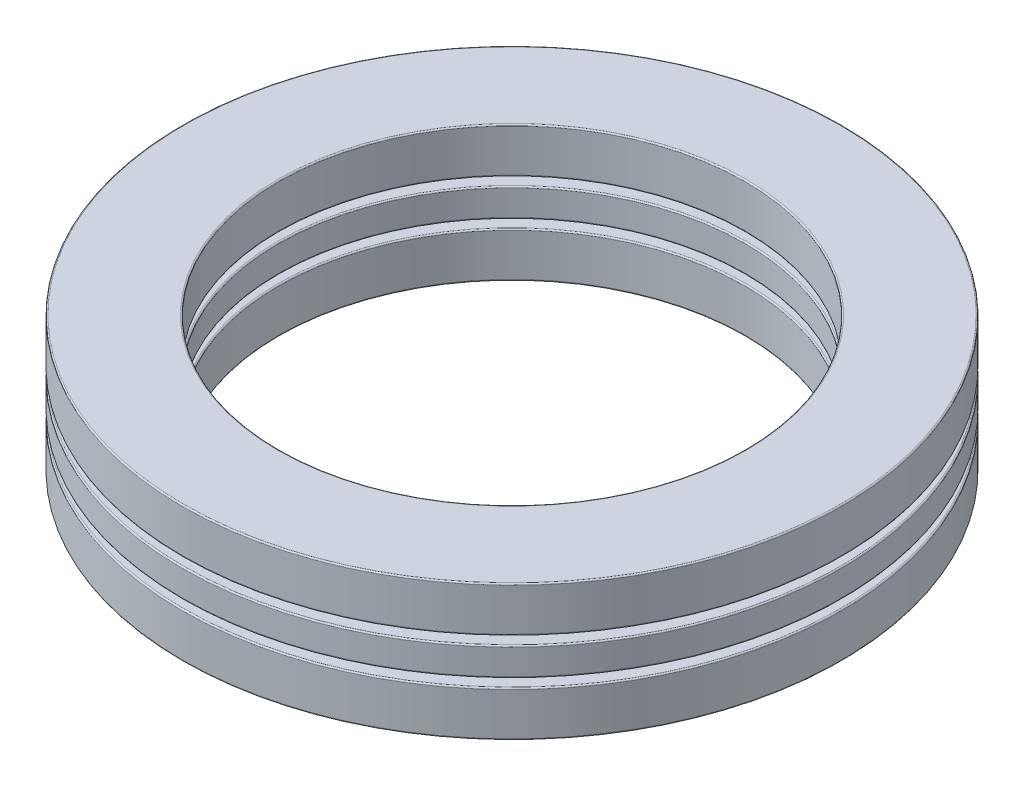
SolidWorks part; units mm, degrees
ref_plane "Front Plane" through (0, 0, 0) normal (0, 0, 1) x (1, 0, 0)
ref_plane "Top Plane" through (0, 0, 0) normal (0, 1, 0) x (1, 0, 0)
ref_plane "Right Plane" through (0, 0, 0) normal (1, 0, 0) x (0, 0, -1)
sketch "Sketch1" plane through (0, 0, 0) normal (1, 0, 0) x (0, 0, -1)
  line L0 (-26.9875, 0) -> (26.9875, 0) construction
  line L1 (0, -5.5499) -> (0, 5.5499) construction
  line L2 (-26.9875, 1.1562) -> (-19.0881, 1.1562)
  line L3 (-26.9875, 1.1562) -> (-26.9875, -1.1562)
  line L4 (-26.9875, -1.1562) -> (-19.0881, -1.1562)
  line L5 (-19.0881, 1.1562) -> (-19.0881, -1.1562)
  line L6 (-23.0378, 1.85) -> (-23.0378, -1.85) construction
  circle A0 centre (-23.0378, 0) radius 1.85 construction
  point P13 (-23.0378, 1.1562)
  dimension "OD" = 53.975
  dimension "Shaft Dia" = 38.1762
  dimension "Th" = 11.0998
  dimension "D1" = 3.6999
  dimension "D2" = 2.3125
revolve "Revolve1" add sketch "Sketch1" angle 360 about L1
sketch "Sketch3" plane through (0, 0, 0) normal (1, 0, 0) x (0, 0, -1)
  line L0 (-23.0378, 1.85) -> (-23.0378, -1.85)
  arc A0 (-23.0378, 1.85) -> (-23.0378, -1.85) centre (-23.0378, 0) ccw
  circle A1 centre (-23.0378, 0) radius 1.85 construction
revolve "Cut-Revolve1" cut sketch "Sketch3" angle 360 about L0
sketch "Sketch2" plane through (0, 0, 0) normal (1, 0, 0) x (0, 0, -1)
  line L0 (-23.0378, 1.85) -> (-23.0378, -1.85)
  arc A0 (-23.0378, 1.85) -> (-23.0378, -1.85) centre (-23.0378, 0) ccw
  circle A2 centre (-23.0378, 0) radius 1.85 construction
revolve "Revolve2" add sketch "Sketch2" angle 360 about L0
ref_axis "Axis1" through (0, 5.5499, 0) along (0, -1, 0)
pattern_circular "CirPattern1" count 11 every 32.727 about axis through (0, 5.5499, 0) along (0, -1, 0) of bodies 187
pattern_circular "CirPattern2" count 11 every 32.727 about axis through (0, 0, 0) along (0, 1, 0) of "Cut-Revolve1"
sketch "Sketch4" plane through (0, 0, 0) normal (1, 0, 0) x (0, 0, -1)
  line L0 (-26.9875, 1.1562) -> (-26.9875, -1.1562) construction
  line L1 (-26.9875, 1.85) -> (-19.0881, 1.85)
  line L2 (-26.9875, 1.85) -> (-26.9875, 5.5499)
  line L3 (-26.9875, 5.5499) -> (-19.0881, 5.5499)
  line L4 (-19.0881, 1.85) -> (-19.0881, 5.5499)
  line L5 (-26.9875, -5.5499) -> (-19.0881, -5.5499)
  line L6 (-26.9875, -5.5499) -> (-26.9875, -1.85)
  line L7 (-26.9875, -1.85) -> (-19.0881, -1.85)
  line L8 (-19.0881, -5.5499) -> (-19.0881, -1.85)
  line L9 (-23.0378, 1.85) -> (-23.0378, -1.85) construction
  line L10 (-19.0881, 1.1562) -> (-19.0881, -1.1562) construction
  line L11 (0, 0) -> (-26.9875, 0) construction
  line L12 (-26.9875, 0) -> (26.9875, 0) construction
  dimension "Ht" = 11.0998
revolve "Revolve3" add sketch "Sketch4" angle 360 about L1
fillet "Fillet1" radius 0.111 4 edges at (0, 1.85, -19.0881) (0, 5.5499, -19.0881) (0, 1.85, -26.9875) (0, 5.5499, -26.9875)
fillet "Fillet2" radius 0.111 4 edges at (0, -1.1562, -19.0881) (0, 1.1562, -19.0881) (0, -1.1562, -26.9875) (0, 1.1562, -26.9875)
fillet "Fillet3" radius 0.111 4 edges at (0, -5.5499, -19.0881) (0, -1.85, -19.0881) (0, -5.5499, -26.9875) (0, -1.85, -26.9875)
equation "\"D1@Sketch1\" = \"Th@Sketch1\"/3"
equation "\"D2@Sketch1\" = \"D1@Sketch1\"*.625"
equation "\"Balls@CirPattern1\" = \"OD@Sketch1\"*5"
equation "\"Angle@CirPattern1\" = 360/\"Balls@CirPattern1\""
equation "\"D1@CirPattern2\" = \"Balls@CirPattern1\""
equation "\"D2@CirPattern2\" = \"Angle@CirPattern1\""
equation "\"D1@Fillet1\" = \"Th@Sketch1\"*.01"
equation "\"D1@Fillet2\" = \"D1@Fillet1\""
equation "\"D1@Fillet3\" = \"D1@Fillet1\""
